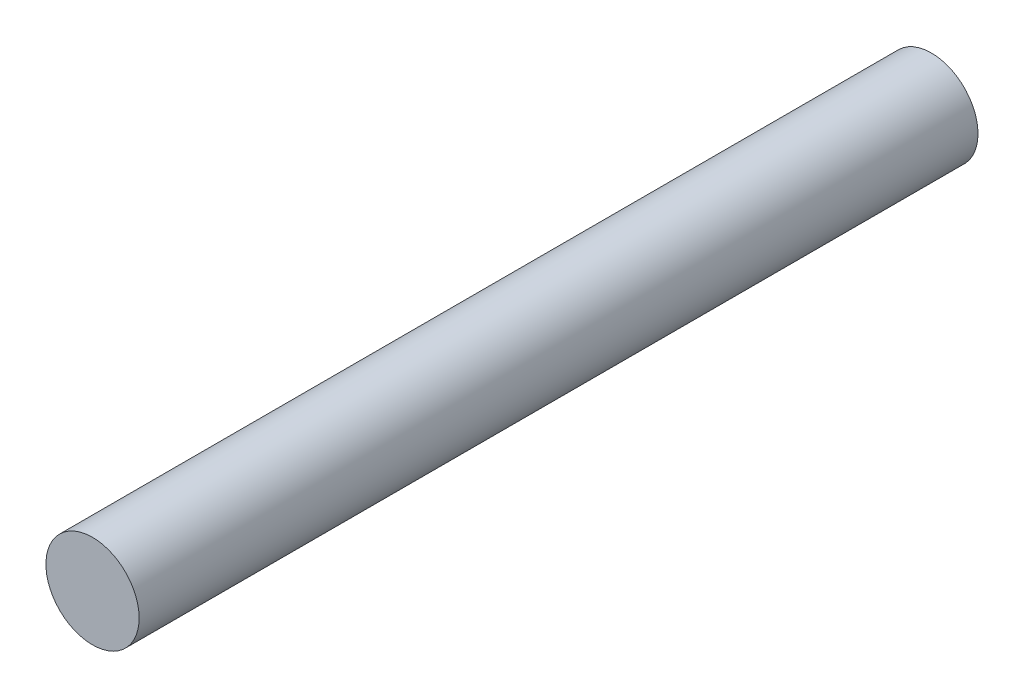
SolidWorks part; units mm, degrees
ref_plane "Front Plane" through (0, 0, 0) normal (0, 0, 1) x (1, 0, 0)
ref_plane "Top Plane" through (0, 0, 0) normal (0, 1, 0) x (1, 0, 0)
ref_plane "Right Plane" through (0, 0, 0) normal (1, 0, 0) x (0, 0, -1)
sketch "Sketch1" plane through (0, 0, 0) normal (0, 0, 1) x (1, 0, 0)
  circle A0 centre (0, 0) radius 1.5875
  dimension "D1" = 3.175
extrude "Boss-Extrude1" add sketch "Sketch1" along normal mid plane 28.575
